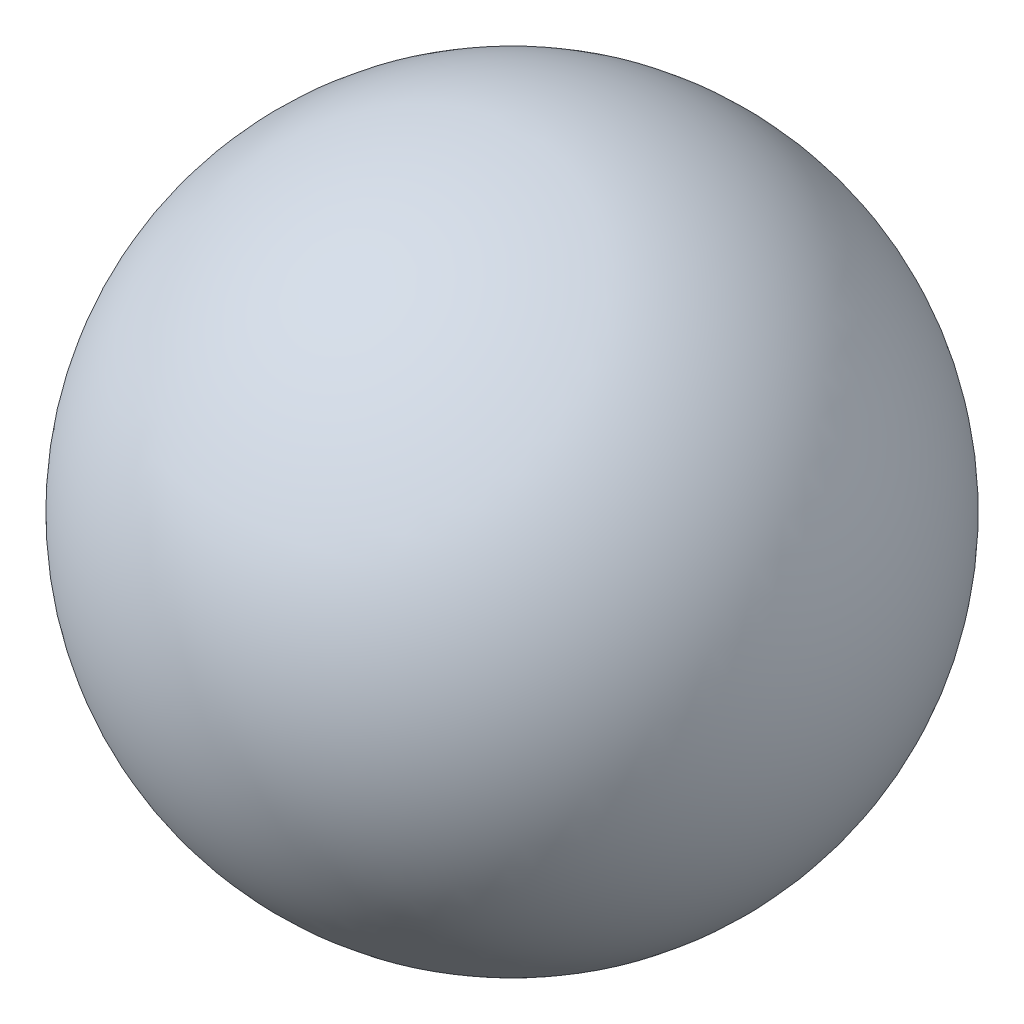
SolidWorks part; units mm, degrees
ref_plane "Front Plane" through (0, 0, 0) normal (0, 0, 1) x (1, 0, 0)
ref_plane "Top Plane" through (0, 0, 0) normal (0, 1, 0) x (1, 0, 0)
ref_plane "Right Plane" through (0, 0, 0) normal (1, 0, 0) x (0, 0, -1)
sketch "Sketch1" plane through (0, 0, 0) normal (0, 0, 1) x (1, 0, 0)
  line L0 (0, 1.5) -> (0, 0)
  line L1 (0, 0) -> (0, -1.5)
  arc A0 (0, 1.5) -> (0, -1.5) centre (0, 0) ccw
  dimension "D1" = 3
revolve "Revolve1" add sketch "Sketch1" angle 360 about L0
